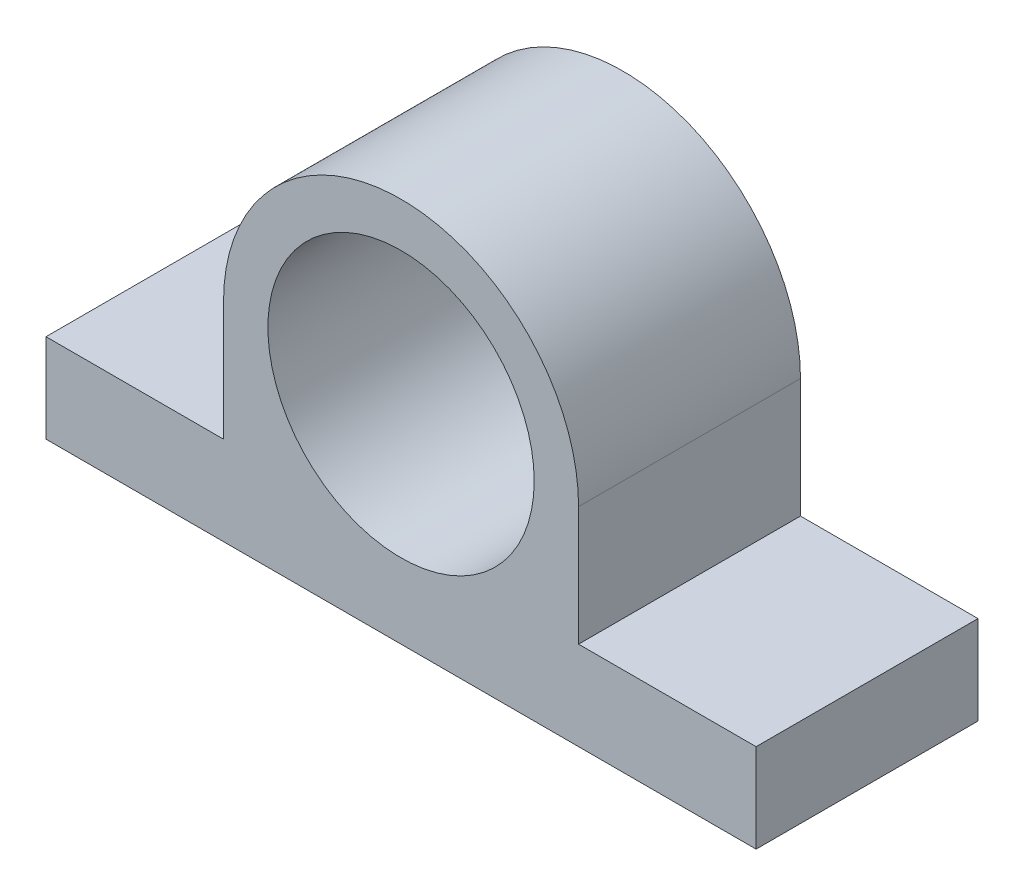
SolidWorks part; units mm, degrees
ref_plane "Front Plane" through (0, 0, 0) normal (0, 0, 1) x (1, 0, 0)
ref_plane "Top Plane" through (0, 0, 0) normal (0, 1, 0) x (1, 0, 0)
ref_plane "Right Plane" through (0, 0, 0) normal (1, 0, 0) x (0, 0, -1)
sketch "Sketch1" plane through (0, 0, 0) normal (0, 0, 1) x (1, 0, 0)
  line L0 (40, 0) -> (-40, 0)
  line L1 (-40, 0) -> (-40, 10)
  line L2 (-40, 10) -> (-20, 10)
  line L3 (-20, 10) -> (-20, 23.4199)
  line L4 (20, 23.4199) -> (20, 10)
  line L5 (20, 10) -> (40, 10)
  line L6 (40, 10) -> (40, 0)
  line L7 (0, 0) -> (0, 13.4199) construction
  arc A0 (-20, 23.4199) -> (20, 23.4199) centre (0, 23.4199) cw
  circle A1 centre (0, 23.4199) radius 15
  point P4 (0, 0)
  dimension "D3" = 30
  dimension "D1" = 10
  dimension "D2" = 80
extrude "Boss-Extrude1" add sketch "Sketch1" along normal blind 25
